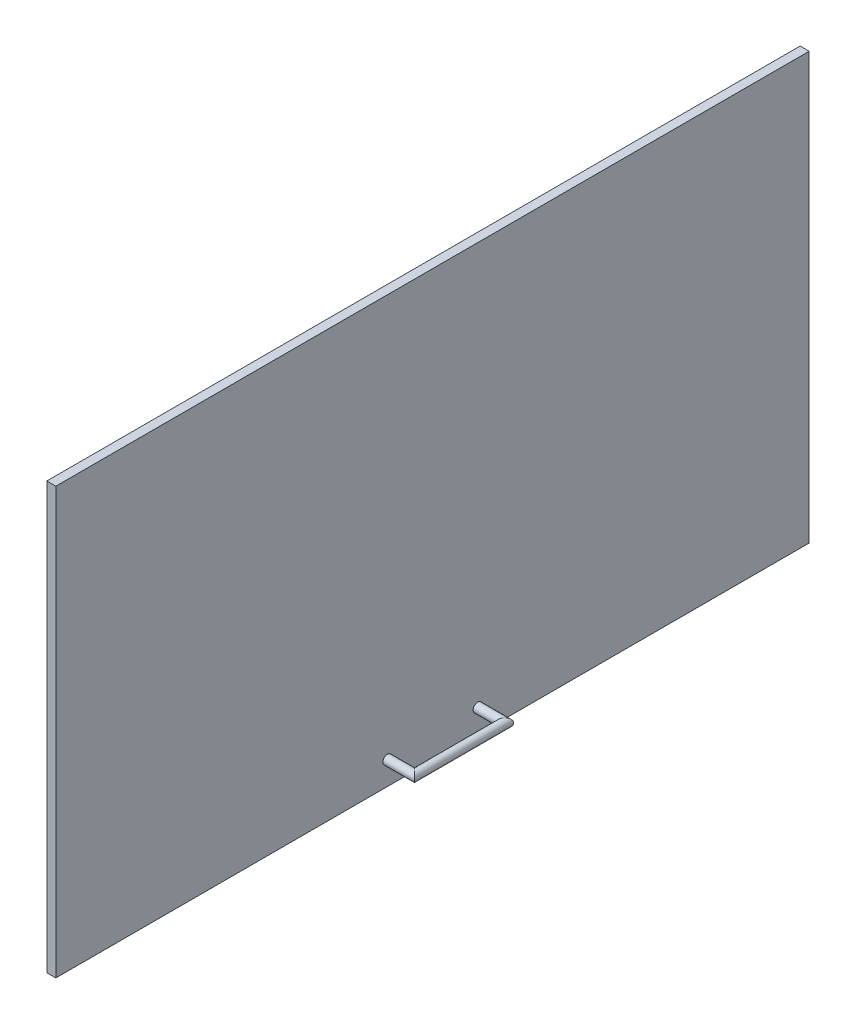
SolidWorks part; units mm, degrees
ref_plane "Front Plane" through (0, 0, 0) normal (0, 0, 1) x (1, 0, 0)
ref_plane "Top Plane" through (0, 0, 0) normal (0, 1, 0) x (1, 0, 0)
ref_plane "Right Plane" through (0, 0, 0) normal (1, 0, 0) x (0, 0, -1)
sketch "Sketch1" plane through (0, 0, 0) normal (1, 0, 0) x (0, 0, -1)
  line L1 (-417.4, -235.955) -> (417.4, -235.955)
  line L2 (-417.4, -235.955) -> (-417.4, 235.955)
  line L3 (-417.4, 235.955) -> (417.4, 235.955)
  line L4 (417.4, -235.955) -> (417.4, 235.955)
  line L5 (-417.4, -235.955) -> (417.4, 235.955) construction
  line L6 (-417.4, 235.955) -> (417.4, -235.955) construction
  point P0 (0, 0)
  dimension "D1" = 471.91
  dimension "D2" = 834.8
extrude "Boss-Extrude1" add sketch "Sketch1" along normal blind 10
sketch "Sketch2" plane through (10, 0, 0) normal (1, 0, 0) x (0, 0, -1)
  line L0 (0, 0) -> (0, -210) construction
  line L1 (-50, -210) -> (50, -210) construction
  circle A0 centre (50, -210) radius 5
  point P6 (0, -210)
  dimension "D1" = 10
  dimension "D2" = 100
  dimension "D3" = 210
sketch3d "3DSketch1"
  line L0 (10, -210, -50) -> (40, -210, -50)
  line L1 (40, -210, -50) -> (40, -210, 50)
  line L2 (10, -210, 50) -> (40, -210, 50)
  point P7 (0, 0, 0)
  dimension "D1" = 30
sweep "Sweep1" add profiles "Sketch2" path "3DSketch1"
